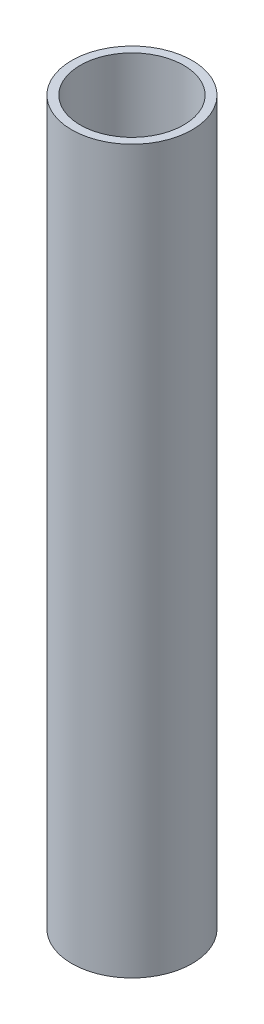
SolidWorks part; units mm, degrees
ref_plane "Спереди" through (0, 0, 0) normal (0, 0, 1) x (1, 0, 0)
ref_plane "Сверху" through (0, 0, 0) normal (0, 1, 0) x (1, 0, 0)
ref_plane "Справа" through (0, 0, 0) normal (1, 0, 0) x (0, 0, -1)
sketch "Эскиз1" plane through (0, 0, 0) normal (0, 1, 0) x (1, 0, 0)
  circle A0 centre (0, 0) radius 25
extrude "Вытянуть-Тонкостенный1" add sketch "Эскиз1" along normal blind 300 thin thin type one direction reverse wall 3.5
